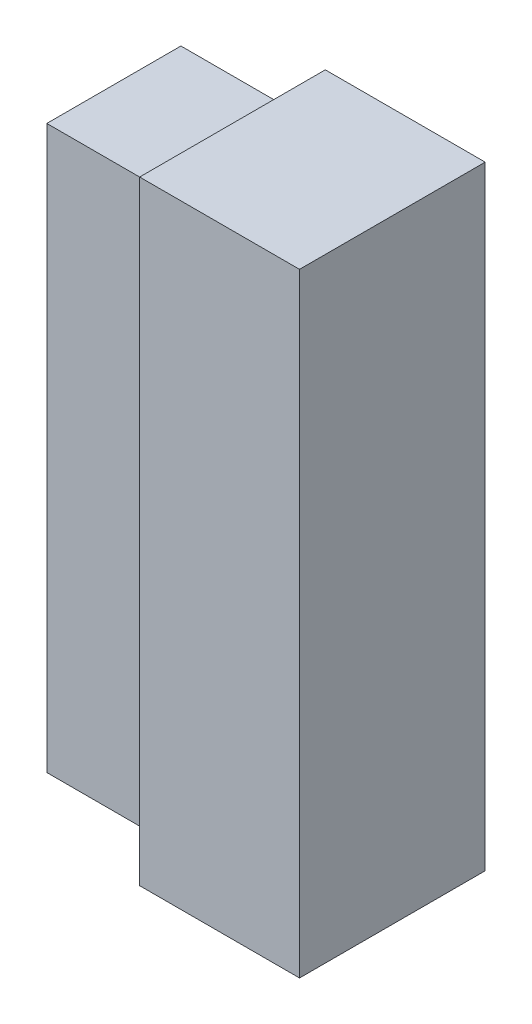
SolidWorks part; units mm, degrees
ref_plane "Front Plane" through (0, 0, 0) normal (0, 0, 1) x (1, 0, 0)
ref_plane "Top Plane" through (0, 0, 0) normal (0, 1, 0) x (1, 0, 0)
ref_plane "Right Plane" through (0, 0, 0) normal (1, 0, 0) x (0, 0, -1)
sketch "Sketch1" plane through (0, 0, 0) normal (0, 1, 0) x (1, 0, 0)
  line L1 (0, 0) -> (31, 0)
  line L2 (0, 0) -> (0, -36)
  line L3 (0, -36) -> (31, -36)
  line L4 (31, 0) -> (31, -36)
  dimension "D1" = 31
  dimension "D2" = 36
extrude "Boss-Extrude1" add sketch "Sketch1" along normal blind 119
sketch "Sketch2" plane through (0, 0, 0) normal (-1, 0, 0) x (0, 0, 1)
  line L8 (5, 5) -> (31, 5)
  line L9 (31, 5) -> (31, 114)
  line L10 (31, 114) -> (5, 114)
  line L11 (5, 114) -> (5, 5)
  line L12 (5, 5) -> (31, 5)
  line L13 (31, 5) -> (31, 114)
  line L14 (31, 114) -> (5, 114)
  line L15 (5, 114) -> (5, 5)
  dimension "D1" = 5
extrude "Boss-Extrude2" add sketch "Sketch2" along normal blind 23
